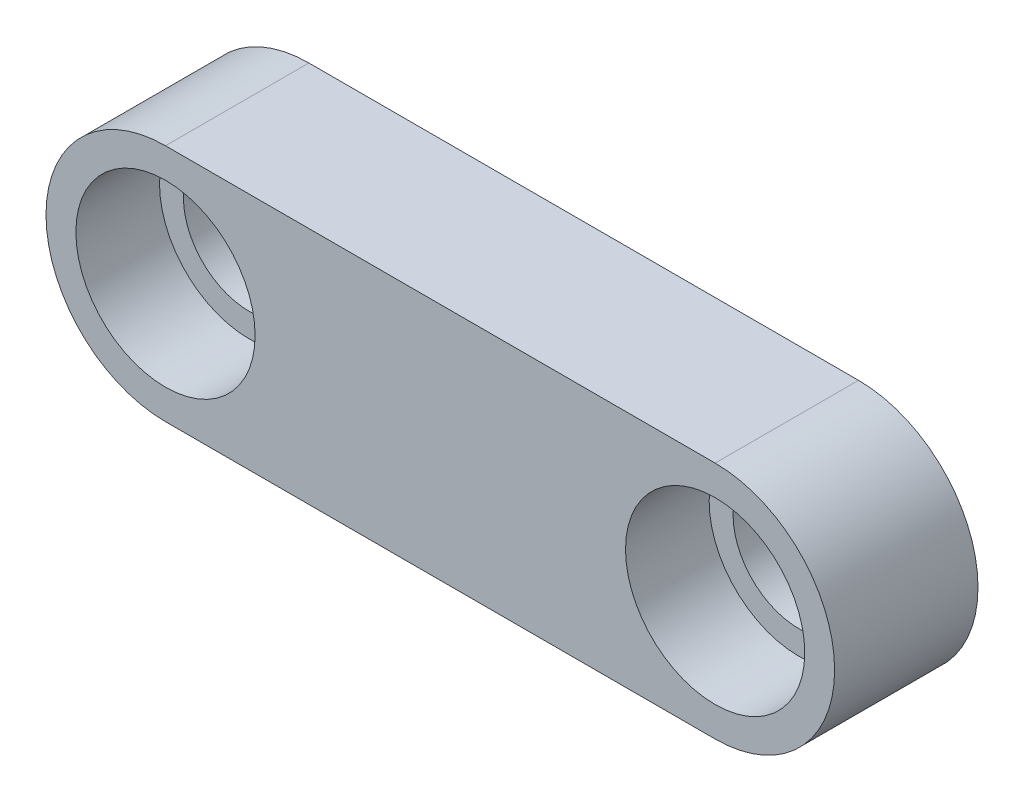
SolidWorks part; units mm, degrees
ref_plane "前视基准面" through (0, 0, 0) normal (0, 0, 1) x (1, 0, 0)
ref_plane "上视基准面" through (0, 0, 0) normal (0, 1, 0) x (1, 0, 0)
ref_plane "右视基准面" through (0, 0, 0) normal (1, 0, 0) x (0, 0, -1)
sketch "草图1" plane through (0, 0, 0) normal (0, 0, 1) x (1, 0, 0)
  line L0 (0, 0) -> (23, 0) construction
  line L1 (0, 5) -> (23, 5)
  line L2 (0, -5) -> (23, -5)
  arc A0 (0, 5) -> (0, -5) centre (0, 0) ccw
  arc A1 (23, -5) -> (23, 5) centre (23, 0) ccw
  point P3 (11.5, 0)
  dimension "D2" = 5
  dimension "D1" = 23
extrude "凸台-拉伸1" add sketch "草图1" along normal blind 6
sketch "草图2" plane through (0, 0, 0) normal (0, 1, 0) x (1, 0, 0)
  line L0 (0, -6) -> (-3.75, -6)
  line L1 (-5, -6) -> (0, -6) construction
  line L2 (-3.75, -6) -> (-3.75, -2.5)
  line L3 (-3.75, -2.5) -> (-2.75, -2.5)
  line L4 (-2.75, -2.5) -> (-2.75, 0)
  line L5 (0, 0) -> (-5, 0) construction
  line L6 (-2.75, 0) -> (0, 0)
  line L7 (0, 0) -> (0, -8.2603) construction
  line L8 (0, -6) -> (0, 0)
  dimension "D1" = 3.75
  dimension "D2" = 3.5
  dimension "D3" = 2.75
revolve "切除-旋转1" cut sketch "草图2" angle 360 about L7
sketch "草图3" plane through (0, 0, 0) normal (0, 1, 0) x (1, 0, 0)
  line L0 (23, -6) -> (19.25, -6)
  line L1 (23, -6) -> (0, -6) construction
  line L2 (19.25, -6) -> (19.25, -2.5)
  line L3 (19.25, -2.5) -> (20.25, -2.5)
  line L4 (20.25, -2.5) -> (20.25, 0)
  line L5 (23, 0) -> (0, 0) construction
  line L6 (20.25, 0) -> (23, 0)
  line L7 (23, 0) -> (23, -6) construction
  line L8 (23, -6) -> (23, 0)
  dimension "D1" = 3.75
  dimension "D2" = 3.5
  dimension "D3" = 2.75
revolve "切除-旋转2" cut sketch "草图3" angle 360 about L7
